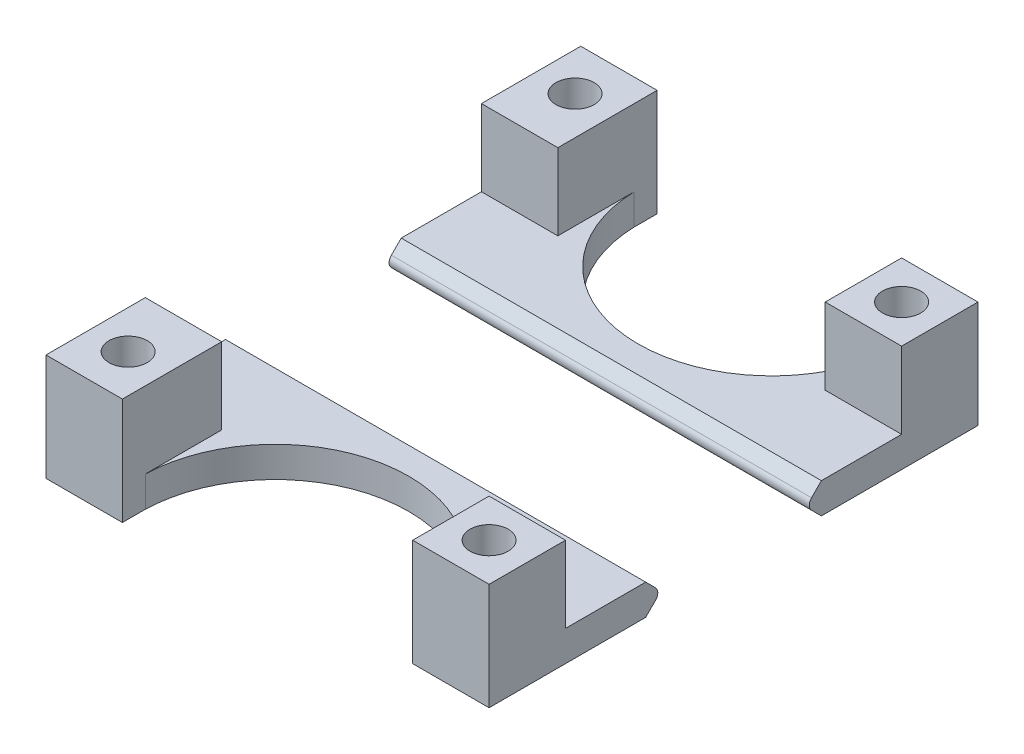
SolidWorks part; units mm, degrees
ref_plane "Front Plane" through (0, 0, 0) normal (0, 0, 1) x (1, 0, 0)
ref_plane "Top Plane" through (0, 0, 0) normal (0, 1, 0) x (1, 0, 0)
ref_plane "Right Plane" through (0, 0, 0) normal (1, 0, 0) x (0, 0, -1)
sketch "Sketch1" plane through (0, 0, 0) normal (0, 1, 0) x (1, 0, 0)
  line L0 (10, 10) -> (10, -10)
  line L2 (0, -20) -> (0, 20)
  line L4 (55, -20) -> (55, 20) construction
  line L5 (10, -10) -> (45, -10)
  line L6 (45, -10) -> (45, 10) construction
  line L7 (45, 10) -> (10, 10)
  line L8 (45, 10) -> (55, 10)
  line L11 (55, 10) -> (55, 20)
  line L13 (27.5, -20) -> (27.5, -10) construction
  line L14 (27.5, 10) -> (27.5, 20) construction
  line L16 (45, -10) -> (55, -10)
  line L17 (55, -20) -> (55, -10)
  line L18 (55, -20) -> (55, -32)
  line L19 (55, -32) -> (45, -32)
  line L20 (0, -32) -> (0, -35)
  line L21 (55, 20) -> (55, 32)
  line L22 (55, 32) -> (45, 32)
  line L23 (0, -35) -> (10, -35)
  line L24 (0, -20) -> (0, -32)
  line L26 (10, -35) -> (10, -32)
  line L27 (0, 20) -> (0, 32)
  line L29 (10, 32) -> (10, 35)
  line L30 (-55, 0) -> (55, 0) construction
  line L31 (0, 0) -> (55, 0) construction
  line L35 (10, 35) -> (0, 35)
  line L36 (0, 35) -> (0, 32)
  arc A26 (45, -32) -> (10, -32) centre (27.5, -32.5074) ccw
  arc A27 (45, 32) -> (10, 32) centre (27.5, 32.5074) cw
  circle A46 centre (50, 27) radius 2.5
  circle A47 centre (50, -27) radius 2.5
  circle A50 centre (5, 29.25) radius 2.5
  circle A52 centre (5, -29.25) radius 2.5
  point P30 (27.5, -15)
  point P35 (27.5, 15)
  point P36 (27.5, -10)
  point P39 (0, 0)
  dimension "D18" = 5
  dimension "D11" = 5
  dimension "D12" = 5
  dimension "D1" = 40
  dimension "D2" = 55
  dimension "D24" = 10
  dimension "D13" = 5
  dimension "D16" = 5
  dimension "D7" = 10
  dimension "D9" = 5
  dimension "D14" = 5
  dimension "D4" = 20
  dimension "D5" = 10
  dimension "D3" = 10
  dimension "D6" = 35
  dimension "D8" = 12
  dimension "D10" = 10
extrude "Extrude-Body" add sketch "Sketch1" along normal blind 4
sketch "Sketch5" plane through (0, 4, 0) normal (0, 1, 0) x (1, 0, 0)
  line L9 (45, -22) -> (55, -22)
  line L21 (55, -22) -> (55, -32)
  line L23 (0, -35) -> (0, 35) construction
  line L36 (55, -32) -> (45, -32)
  line L37 (45, -32) -> (45, -22)
  line L38 (55, 22) -> (55, 32)
  line L39 (55, 32) -> (45, 32)
  line L41 (45, 32) -> (45, 22)
  line L42 (45, 22) -> (55, 22)
  line L43 (10, 22) -> (10, 35)
  line L45 (10, 35) -> (0, 35)
  line L46 (0, 35) -> (0, 22)
  line L47 (0, -35) -> (0, 35) construction
  line L48 (0, 22) -> (10, 22)
  line L49 (10, -22) -> (0, -22)
  line L50 (0, -22) -> (0, -35)
  line L52 (10, -35) -> (10, -22)
  line L55 (10, -35) -> (0, -35)
  circle A0 centre (50, 27) radius 2.5
  circle A3 centre (50, -27) radius 2.5
  circle A11 centre (50, 27) radius 2.5 construction
  circle A12 centre (50, -27) radius 2.5 construction
  circle A13 centre (5, -29.25) radius 2.5 construction
  circle A14 centre (5, -29.25) radius 2.5
  circle A15 centre (5, 29.25) radius 2.5 construction
  circle A16 centre (5, 29.25) radius 2.5
  dimension "D1" = 10
  dimension "D2" = 10
  dimension "D3" = 10
  dimension "D4" = 10
  dimension "D5" = 10
  dimension "D6" = 10
  dimension "D8" = 13
extrude "Extrude-Legs" add sketch "Sketch5" along normal blind 10
sketch "Sketch6" plane through (0, 4, 0) normal (0, 1, 0) x (1, 0, 0)
  line L0 (55, -10) -> (55, -22) construction
  line L1 (10, -10) -> (55, -10)
  line L2 (10, -10) -> (10, -9.5)
  line L3 (10, -9.5) -> (55, -9.5)
  line L4 (55, -10) -> (55, -9.5)
  line L5 (10, 10) -> (55, 10)
  line L6 (10, 10) -> (10, 9.5)
  line L7 (10, 9.5) -> (55, 9.5)
  line L8 (55, 10) -> (55, 9.5)
  line L9 (55, 10) -> (55, 22) construction
  dimension "D1" = 19
extrude "Boss-Extrude1" add sketch "Sketch6" against normal up to surface (4 mm away) up to face at (5, 0, 31.75)
sketch "Sketch7" plane through (55, 0, 0) normal (1, 0, 0) x (0, 0, -1)
  line L0 (-10.2071, 2.7071) -> (-11.5, 4)
  line L1 (-9.5, 0) -> (-9.5, 4) construction
  line L2 (-9.5, 4) -> (-22, 4) construction
  line L3 (-10.2071, 1.2929) -> (-11.5, 0)
  line L4 (-9.5, 0) -> (-32, 0) construction
  line L5 (10.2071, 2.7071) -> (11.5, 4)
  line L6 (9.5, 0) -> (9.5, 4) construction
  line L7 (9.5, 4) -> (22, 4) construction
  line L8 (10.2071, 1.2929) -> (11.5, 0)
  line L9 (9.5, 0) -> (32, 0) construction
  line L10 (11.5, 4) -> (9.5, 4)
  line L11 (9.5, 0) -> (9.5, 4) construction
  line L12 (9.5, 4) -> (9.5, 0)
  line L13 (9.5, 0) -> (11.5, 0)
  line L14 (-11.5, 4) -> (-9.5, 4)
  line L15 (-9.5, 4) -> (-9.5, 0)
  line L16 (-9.5, 0) -> (-11.5, 0)
  line L17 (0, 0) -> (0, 8.2974) construction
  arc A0 (10.2071, 2.7071) -> (10.2071, 1.2929) centre (10.9142, 2) ccw
  arc A1 (-10.2071, 2.7071) -> (-10.2071, 1.2929) centre (-10.9142, 2) cw
  point P36 (9.5, 2)
  point P39 (-9.5, 2)
  dimension "D3" = 1
  dimension "D1" = 45
  dimension "D2" = 45
extrude "Cut-Extrude1" cut sketch "Sketch7" against normal up to surface (55 mm away) up to face at (0, 8, 0)
sketch "Sketch8" plane through (0, 4, 0) normal (0, 1, 0) x (1, 0, 0)
  line L0 (10, 9.5) -> (10, -9.5) construction
  line L1 (0, -9.5) -> (10, -9.5)
  line L2 (0, -9.5) -> (0, 9.5)
  line L3 (0, 9.5) -> (10, 9.5)
  line L4 (10, -9.5) -> (10, 9.5)
extrude "Cut-Extrude2" cut sketch "Sketch8" against normal blind 10
equation "\"boltdiameter\"=5"
equation "\"D18@Sketch1\"=\"boltdiameter\""
equation "\"boltfacediameter\"=7"
equation "\"insetNutFlat\"=8.4"
equation "\"screwInset\"=8.43"
equation "\"slotLength\"=80"
equation "\"D11@Sketch1\"=\"boltdiameter\""
equation "\"D12@Sketch1\"=\"boltdiameter\""
